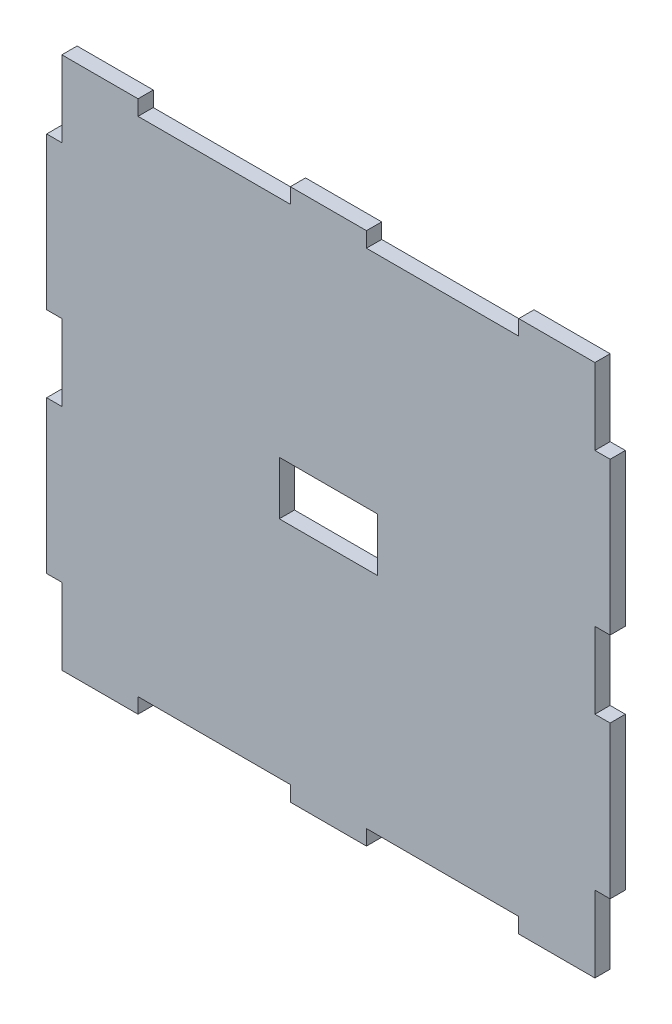
SolidWorks part; units mm, degrees
ref_plane "Front Plane" through (0, 0, 0) normal (0, 0, 1) x (1, 0, 0)
ref_plane "Top Plane" through (0, 0, 0) normal (0, 1, 0) x (1, 0, 0)
ref_plane "Right Plane" through (0, 0, 0) normal (1, 0, 0) x (0, 0, -1)
sketch "Sketch1" plane through (0, 0, 0) normal (0, 0, 1) x (1, 0, 0)
  line L1 (-35, -35) -> (35, -35)
  line L2 (-35, -35) -> (-35, 35)
  line L3 (-35, 35) -> (35, 35)
  line L4 (35, -35) -> (35, 35)
  line L5 (0, 35) -> (0, -35) construction
  line L6 (-35, 0) -> (35, 0) construction
  line L11 (0, 18) -> (0, -18) construction
  line L12 (-17.25, 0) -> (17.25, 0) construction
  point P0 (0, 0)
  point P4 (0, 0)
  dimension "D1" = 70
  dimension "D2" = 70
extrude "Boss-Extrude1" add sketch "Sketch1" against normal blind 2
sketch "Sketch2" plane through (0, 0, 0) normal (0, 0, 1) x (1, 0, 0)
  line L0 (-35, 35) -> (-25, 35)
  line L1 (35, 35) -> (-35, 35) construction
  line L2 (-25, 35) -> (-5, 35)
  line L3 (-5, 35) -> (5, 35)
  line L4 (5, 35) -> (25, 35)
  line L6 (35, 35) -> (35, 25)
  line L7 (-25, 33) -> (-5, 33)
  line L8 (-25, 33) -> (-25, 37)
  line L9 (-25, 37) -> (-5, 37)
  line L10 (-5, 33) -> (-5, 37)
  line L11 (-15, 37) -> (-15, 33) construction
  line L12 (-25, 35) -> (-5, 35) construction
  line L13 (5, 33) -> (25, 33)
  line L14 (5, 33) -> (5, 37)
  line L15 (5, 37) -> (25, 37)
  line L16 (25, 33) -> (25, 37)
  line L17 (15, 37) -> (15, 33) construction
  line L18 (5, 35) -> (25, 35) construction
  line L19 (35, -35) -> (35, 35) construction
  line L20 (35, 25) -> (35, 5)
  line L21 (35, 5) -> (35, -5)
  line L22 (35, -5) -> (35, -25)
  line L23 (-35, -35) -> (-25, -35)
  line L24 (35, -5) -> (33, -5)
  line L25 (35, -5) -> (35, -25)
  line L26 (35, -25) -> (33, -25)
  line L27 (33, -5) -> (33, -25)
  line L28 (35, 25) -> (33, 25)
  line L29 (35, 25) -> (35, 5)
  line L30 (35, 5) -> (33, 5)
  line L31 (33, 25) -> (33, 5)
  line L32 (-35, -35) -> (35, -35) construction
  line L33 (-25, -35) -> (-5, -35)
  line L34 (-5, -35) -> (5, -35)
  line L35 (5, -35) -> (25, -35)
  line L36 (-35, 35) -> (-35, 25)
  line L37 (-25, -35) -> (-5, -35)
  line L38 (-25, -35) -> (-25, -33)
  line L39 (-25, -33) -> (-5, -33)
  line L40 (-5, -35) -> (-5, -33)
  line L41 (5, -35) -> (25, -35)
  line L42 (5, -35) -> (5, -33)
  line L43 (5, -33) -> (25, -33)
  line L44 (25, -35) -> (25, -33)
  line L45 (-35, 35) -> (-35, -35) construction
  line L46 (-35, 25) -> (-35, 5)
  line L47 (-35, 5) -> (-35, -5)
  line L48 (-35, -5) -> (-35, -25)
  line L49 (-35, 25) -> (-37, 25)
  line L50 (-35, 25) -> (-33, 25)
  line L51 (-35, 25) -> (-35, 5)
  line L52 (-35, 5) -> (-33, 5)
  line L53 (-33, 25) -> (-33, 5)
  line L54 (-35, -5) -> (-33, -5)
  line L55 (-35, -5) -> (-35, -25)
  line L56 (-35, -25) -> (-33, -25)
  line L57 (-33, -5) -> (-33, -25)
  line L58 (-35, 25) -> (-35, 5)
  line L59 (-35, 5) -> (-37, 5)
  line L60 (-37, 25) -> (-37, 5)
  line L61 (-35, -5) -> (-37, -5)
  line L62 (-35, -5) -> (-35, -25)
  line L63 (-35, -25) -> (-37, -25)
  line L64 (-37, -5) -> (-37, -25)
  line L65 (-25, -35) -> (-5, -35)
  line L66 (-25, -35) -> (-25, -37)
  line L67 (-25, -37) -> (-5, -37)
  line L68 (-5, -35) -> (-5, -37)
  line L69 (5, -35) -> (25, -35)
  line L70 (5, -35) -> (5, -37)
  line L71 (5, -37) -> (25, -37)
  line L72 (25, -35) -> (25, -37)
  line L73 (35, -25) -> (37, -25)
  line L74 (35, -25) -> (35, -5)
  line L75 (35, -5) -> (37, -5)
  line L76 (37, -25) -> (37, -5)
  line L77 (35, 5) -> (37, 5)
  line L78 (35, 5) -> (35, 25)
  line L79 (35, 25) -> (37, 25)
  line L80 (37, 5) -> (37, 25)
  point P7 (15, 35)
  point P9 (-15, 35)
  point P10 (-15, 35)
  point P14 (15, 35)
  line M25 (35, -35) -> (35, 35)
  line M27 (-35, 35) -> (-35, -35)
  dimension "D1" = 10
  dimension "D2" = 20
  dimension "D3" = 10
  dimension "D4" = 20
  dimension "D5" = 4
  dimension "D6" = 20
  dimension "D7" = 20
  dimension "D8" = 4
  dimension "D9" = 10
  dimension "D10" = 20
  dimension "D11" = 10
  dimension "D12" = 20
  dimension "D13" = 2
  dimension "D14" = 2
  dimension "D15" = 10
  dimension "D16" = 20
  dimension "D17" = 10
  dimension "D18" = 20
  dimension "D19" = 20
  dimension "D20" = 20
  dimension "D21" = 2
  dimension "D22" = 2
  dimension "D23" = 10
  dimension "D24" = 20
  dimension "D25" = 10
  dimension "D26" = 20
  dimension "D27" = 2
  dimension "D28" = 2
  dimension "D29" = 2
  dimension "D30" = 2
  dimension "D31" = 2
  dimension "D32" = 2
  dimension "D33" = 2
  dimension "D34" = 2
sketch "Sketch3" plane through (0, 0, 0) normal (0, 0, 1) x (1, 0, 0)
  line L0 (-35, 35) -> (-25, 35)
  line L2 (-25, 35) -> (-5, 35)
  line L3 (-5, 35) -> (5, 35)
  line L4 (5, 35) -> (25, 35)
  line L6 (35, 35) -> (35, 25)
  line L7 (-25, 33) -> (-5, 33)
  line L8 (-25, 33) -> (-25, 37)
  line L9 (-25, 37) -> (-5, 37)
  line L10 (-5, 33) -> (-5, 37)
  line L11 (-15, 37) -> (-15, 33) construction
  line L12 (-25, 35) -> (-5, 35) construction
  line L13 (5, 33) -> (25, 33)
  line L14 (5, 33) -> (5, 37)
  line L15 (5, 37) -> (25, 37)
  line L16 (25, 33) -> (25, 37)
  line L17 (15, 37) -> (15, 33) construction
  line L18 (5, 35) -> (25, 35) construction
  line L20 (35, 25) -> (35, 5)
  line L21 (35, 5) -> (35, -5)
  line L22 (35, -5) -> (35, -25)
  line L23 (-35, -35) -> (-25, -35)
  line L24 (35, -5) -> (33, -5)
  line L25 (35, -5) -> (35, -25)
  line L26 (35, -25) -> (33, -25)
  line L27 (33, -5) -> (33, -25)
  line L28 (35, 25) -> (33, 25)
  line L29 (35, 25) -> (35, 5)
  line L30 (35, 5) -> (33, 5)
  line L31 (33, 25) -> (33, 5)
  line L33 (-25, -35) -> (-5, -35)
  line L34 (-5, -35) -> (5, -35)
  line L35 (5, -35) -> (25, -35)
  line L36 (-35, 35) -> (-35, 25)
  line L37 (-25, -35) -> (-5, -35)
  line L38 (-25, -35) -> (-25, -33)
  line L39 (-25, -33) -> (-5, -33)
  line L40 (-5, -35) -> (-5, -33)
  line L41 (5, -35) -> (25, -35)
  line L42 (5, -35) -> (5, -33)
  line L43 (5, -33) -> (25, -33)
  line L44 (25, -35) -> (25, -33)
  line L46 (-35, 25) -> (-35, 5)
  line L47 (-35, 5) -> (-35, -5)
  line L48 (-35, -5) -> (-35, -25)
  line L49 (-35, 25) -> (-37, 25)
  line L50 (-35, 25) -> (-33, 25)
  line L51 (-35, 25) -> (-35, 5)
  line L52 (-35, 5) -> (-33, 5)
  line L53 (-33, 25) -> (-33, 5)
  line L54 (-35, -5) -> (-33, -5)
  line L55 (-35, -5) -> (-35, -25)
  line L56 (-35, -25) -> (-33, -25)
  line L57 (-33, -5) -> (-33, -25)
  line L58 (-35, 25) -> (-35, 5)
  line L59 (-35, 5) -> (-37, 5)
  line L60 (-37, 25) -> (-37, 5)
  line L61 (-35, -5) -> (-37, -5)
  line L62 (-35, -5) -> (-35, -25)
  line L63 (-35, -25) -> (-37, -25)
  line L64 (-37, -5) -> (-37, -25)
  line L65 (-25, -35) -> (-5, -35)
  line L66 (-25, -35) -> (-25, -37)
  line L67 (-25, -37) -> (-5, -37)
  line L68 (-5, -35) -> (-5, -37)
  line L69 (5, -35) -> (25, -35)
  line L70 (5, -35) -> (5, -37)
  line L71 (5, -37) -> (25, -37)
  line L72 (25, -35) -> (25, -37)
  line L73 (35, -25) -> (37, -25)
  line L74 (35, -25) -> (35, -5)
  line L75 (35, -5) -> (37, -5)
  line L76 (37, -25) -> (37, -5)
  line L77 (35, 5) -> (37, 5)
  line L78 (35, 5) -> (35, 25)
  line L79 (35, 25) -> (37, 25)
  line L80 (37, 5) -> (37, 25)
  point P7 (15, 35)
  point P9 (-15, 35)
  point P10 (-15, 35)
  point P14 (15, 35)
  dimension "D1" = 10
  dimension "D2" = 20
  dimension "D3" = 10
  dimension "D4" = 20
  dimension "D5" = 4
  dimension "D6" = 20
  dimension "D7" = 20
  dimension "D8" = 4
  dimension "D9" = 10
  dimension "D10" = 20
  dimension "D11" = 10
  dimension "D12" = 20
  dimension "D13" = 2
  dimension "D14" = 2
  dimension "D15" = 10
  dimension "D16" = 20
  dimension "D17" = 10
  dimension "D18" = 20
  dimension "D19" = 20
  dimension "D20" = 20
  dimension "D21" = 2
  dimension "D22" = 2
  dimension "D23" = 10
  dimension "D24" = 20
  dimension "D25" = 10
  dimension "D26" = 20
  dimension "D27" = 2
  dimension "D28" = 2
  dimension "D29" = 2
  dimension "D30" = 2
  dimension "D31" = 2
  dimension "D32" = 2
  dimension "D33" = 2
  dimension "D34" = 2
extrude "Boss-Extrude2" add sketch "Sketch2" against normal blind 2 contours L49 L60 L59 M27 | L61 L64 L63 M27 | L73 L76 L75 M25 | L77 L80 L79 M25
extrude "Cut-Extrude1" cut sketch "Sketch3" against normal blind 2 contours L7 L10 L2 L8 | L13 L16 L4 L14 | L33 L40 L39 L38 | L35 L44 L43 L42
sketch "Sketch4" plane through (0, 0, 0) normal (0, 0, 1) x (1, 0, 0)
  line L1 (-6.45, -3.5) -> (6.45, -3.5)
  line L2 (-6.45, -3.5) -> (-6.45, 3.5)
  line L3 (-6.45, 3.5) -> (6.45, 3.5)
  line L4 (6.45, -3.5) -> (6.45, 3.5)
  line L5 (0, 3.5) -> (0, -3.5) construction
  line L6 (-6.45, 0) -> (6.45, 0) construction
  point P0 (0, 0)
  dimension "D1" = 12.9
  dimension "D2" = 7
extrude "Cut-Extrude2" cut sketch "Sketch4" against normal blind 10
